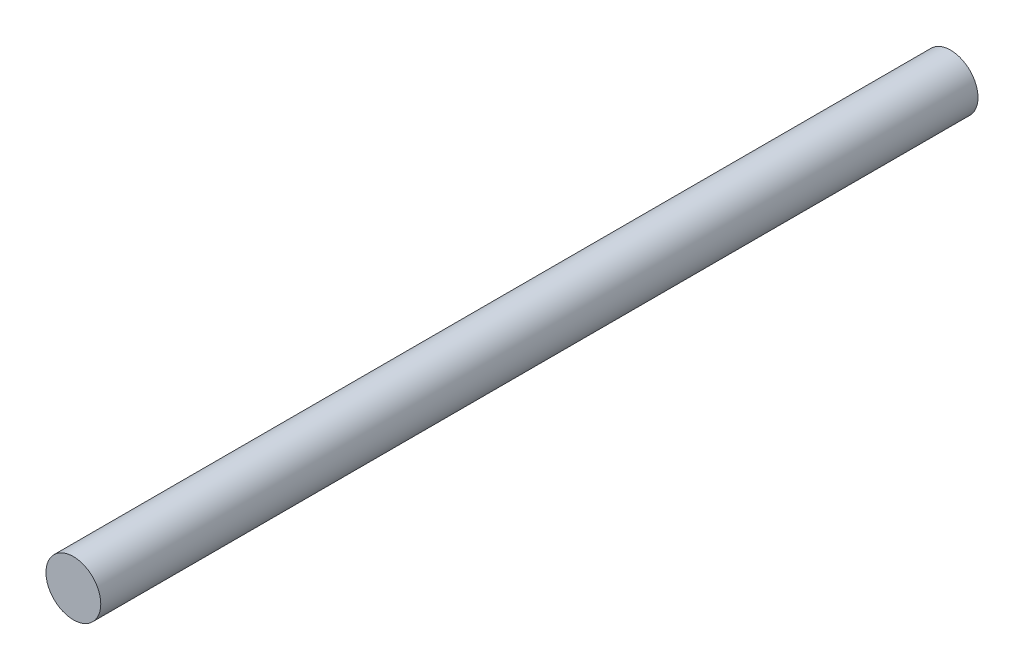
SolidWorks part; units mm, degrees
ref_plane "Front Plane" through (0, 0, 0) normal (0, 0, 1) x (1, 0, 0)
ref_plane "Top Plane" through (0, 0, 0) normal (0, 1, 0) x (1, 0, 0)
ref_plane "Right Plane" through (0, 0, 0) normal (1, 0, 0) x (0, 0, -1)
sketch "Sketch1" plane through (0, 0, 0) normal (0, 0, 1) x (1, 0, 0)
  circle A0 centre (0, 0) radius 3.175
  dimension "D1" = 6.35
extrude "Boss-Extrude1" add sketch "Sketch1" along normal mid plane 101.6
